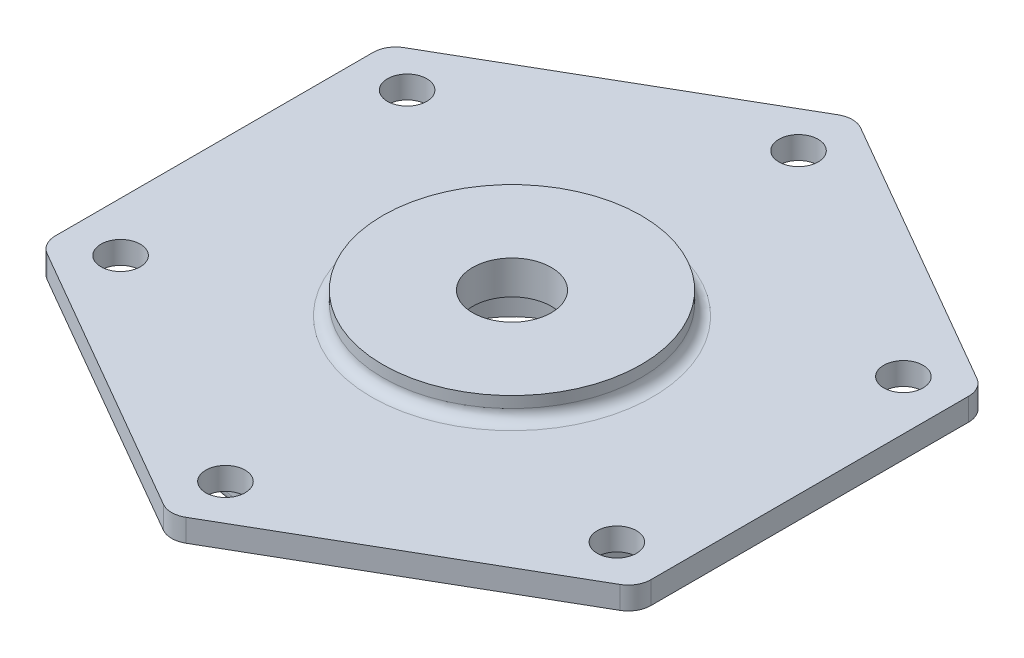
SolidWorks part; units mm, degrees
ref_plane "Front Plane" through (0, 0, 0) normal (0, 0, 1) x (1, 0, 0)
ref_plane "Top Plane" through (0, 0, 0) normal (0, 1, 0) x (1, 0, 0)
ref_plane "Right Plane" through (0, 0, 0) normal (1, 0, 0) x (0, 0, -1)
sketch "Sketch1" plane through (0, 0, 0) normal (0, 1, 0) x (1, 0, 0)
  line L1 (-2, 60.0444) -> (-51, 31.7543)
  line L2 (-53, 28.2902) -> (-53, -28.2902)
  line L3 (-51, -31.7543) -> (-2, -60.0444)
  line L4 (2, -60.0444) -> (51, -31.7543)
  line L5 (53, -28.2902) -> (53, 28.2902)
  line L6 (51, 31.7543) -> (2, 60.0444)
  circle A0 centre (0, 0) radius 53 construction
  arc A1 (53, 28.2902) -> (51, 31.7543) centre (49, 28.2902) ccw
  arc A2 (51, -31.7543) -> (53, -28.2902) centre (49, -28.2902) ccw
  arc A3 (-2, -60.0444) -> (2, -60.0444) centre (0, -56.5803) ccw
  arc A4 (-53, -28.2902) -> (-51, -31.7543) centre (-49, -28.2902) ccw
  arc A5 (-51, 31.7543) -> (-53, 28.2902) centre (-49, 28.2902) ccw
  arc A6 (-2, 60.0444) -> (2, 60.0444) centre (0, 56.5803) cw
  point P21 (0, 61.1991)
  dimension "D2" = 4
  dimension "D1" = 106
extrude "Boss-Extrude1" add sketch "Sketch1" along normal blind 4
sketch "Sketch2" plane through (0, 4, 0) normal (0, 1, 0) x (1, 0, 0)
  circle A0 centre (0, 0) radius 23
  dimension "D1" = 46
extrude "Boss-Extrude2" add sketch "Sketch2" along normal blind 4
sketch "Sketch3" plane through (0, 0, 0) normal (0, -1, 0) x (1, 0, 0)
  circle A0 centre (0, 0) radius 45
  dimension "D1" = 90
extrude "Boss-Extrude3" add sketch "Sketch3" along normal blind 6
sketch "Sketch4" plane through (0, -6, 0) normal (0, -1, 0) x (1, 0, 0)
  circle A0 centre (0, 0) radius 40
  circle A1 centre (0, 0) radius 19
  dimension "D1" = 80
  dimension "D2" = 38
extrude "Cut-Extrude1" cut sketch "Sketch4" against normal blind 6
sketch "Sketch5" plane through (0, -6, 0) normal (0, -1, 0) x (1, 0, 0)
  circle A0 centre (0, 0) radius 14
  dimension "D1" = 28
extrude "Cut-Extrude2" cut sketch "Sketch5" against normal blind 8
sketch "Sketch6" plane through (0, 2, 0) normal (0, -1, 0) x (1, 0, 0)
  circle A0 centre (0, 0) radius 7
  dimension "D1" = 14
extrude "Cut-Extrude3" cut sketch "Sketch6" against normal through all
fillet "Fillet1" radius 2 3 edges at (0, 4, 23) (0, -6, -45) (0, -6, -19)
sketch "Sketch7" plane through (0, 4, 0) normal (0, 1, 0) x (1, 0, 0)
  circle A0 centre (0, 0) radius 51 construction
  circle A1 centre (0, 51) radius 3.5
  circle A2 centre (44.1673, 25.5) radius 3.5
  circle A3 centre (44.1673, -25.5) radius 3.5
  circle A4 centre (0, -51) radius 3.5
  circle A5 centre (-44.1673, -25.5) radius 3.5
  circle A6 centre (-44.1673, 25.5) radius 3.5
  dimension "D1" = 102
  dimension "D2" = 7
  dimension "D3" = 6
extrude "Cut-Extrude4" cut sketch "Sketch7" against normal through all
